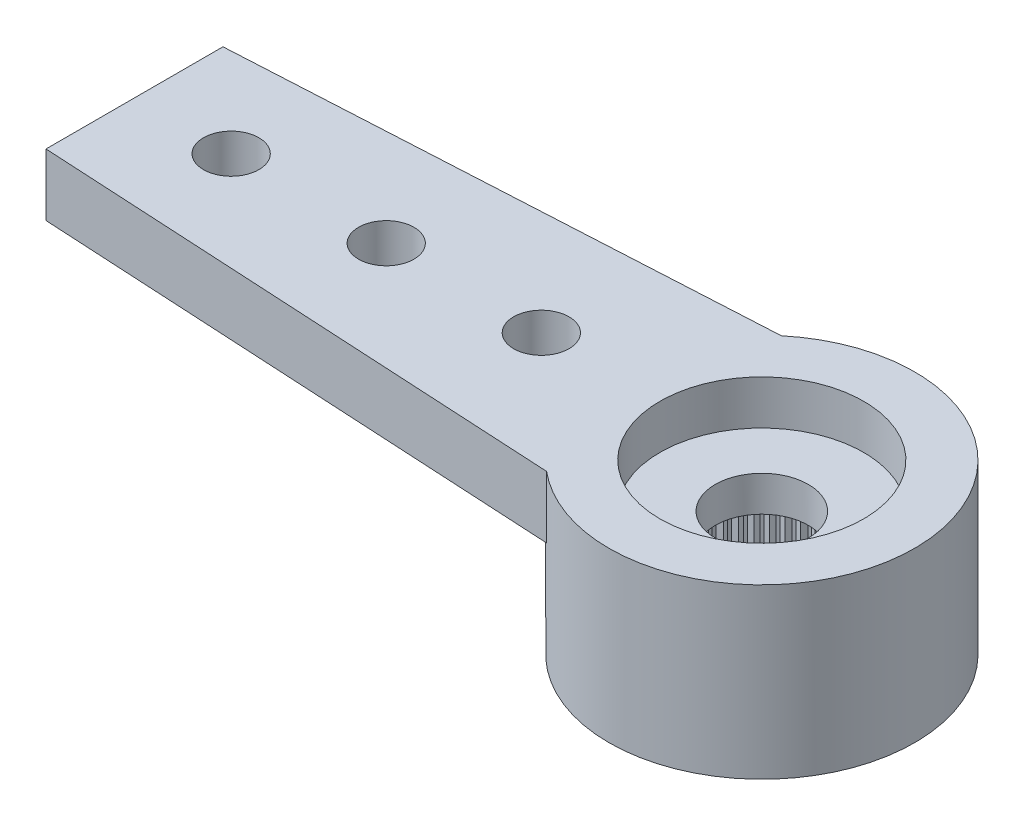
SolidWorks part; units mm, degrees
material "PVC Rígido"
ref_plane "Plano frontal" through (0, 0, 0) normal (0, 0, 1) x (1, 0, 0)
ref_plane "Plano superior" through (0, 0, 0) normal (0, 1, 0) x (1, 0, 0)
ref_plane "Plano direito" through (0, 0, 0) normal (1, 0, 0) x (0, 0, -1)
sketch "Esboço1" plane through (0, 0, 0) normal (0, 1, 0) x (1, 0, 0)
  line L0 (0, 0) -> (-15.7115, 0) construction
  line L1 (-14.1591, 1.997) -> (-2.2091, 2.65)
  line L2 (-2.2091, -2.65) -> (-14.1591, -1.997)
  line L3 (-14.1591, -1.997) -> (-14.1591, 1.997)
  arc A0 (-2.2091, -2.65) -> (-2.2091, 2.65) centre (0, 0) ccw
  dimension "D1" = 6.9
  dimension "D4" = 5.3
extrude "Ressalto-extrusão1" add sketch "Esboço1" against normal blind 1.4
sketch "Esboço2" plane through (0, -1.4, 0) normal (0, -1, 0) x (1, 0, 0)
  arc A0 (-2.2091, -2.65) -> (-2.2091, 2.65) centre (0, 0) ccw construction
  circle A1 centre (0, 0) radius 3.45
extrude "Ressalto-extrusão2" add sketch "Esboço2" along normal offset from surface (2.4 mm away) 3.8 up to face at (-6.7693, 0, 0)
hole_wizard "Furo1" positions "Esboço3" profile "Esboço4" legacy
sketch "Esboço3" plane through (0, -3.8, 0) normal (0, -1, 0) x (-1, 0, 0)
  point P0 (0, 0)
sketch "Esboço4" plane through (0, -3.8, 0) normal (1, 0, 0) x (0, 0, -1)
  line L0 (0, 0) -> (0, 2)
  line L1 (0, 2) -> (2.475, 2)
  line L2 (2.475, 2) -> (2.475, 0)
  line L3 (2.475, 0) -> (0, 0)
  line L4 (0, 110) -> (0, -10) construction
  dimension "Diameter" = 4.95
  dimension "Depth" = 2
hole_wizard "Furo2" positions "Esboço5" profile "Esboço6" legacy
sketch "Esboço5" plane through (0, 0, 0) normal (0, 1, 0) x (1, 0, 0)
  point P0 (0, 0)
sketch "Esboço6" plane through (0, 0, 0) normal (1, 0, 0) x (0, 0, 1)
  line L0 (0, 0) -> (0, 1)
  line L1 (0, 1) -> (2.3, 1)
  line L2 (2.3, 1) -> (2.3, 0)
  line L3 (2.3, 0) -> (0, 0)
  line L4 (0, 110) -> (0, -10) construction
  dimension "Diameter" = 4.6
  dimension "Depth" = 1
hole_wizard "Furo3" positions "Esboço7" profile "Esboço8" legacy end condition through all
sketch "Esboço7" plane through (0, 0, 0) normal (0, 1, 0) x (1, 0, 0)
  point P0 (0, 0)
sketch "Esboço8" plane through (0, 0, 0) normal (1, 0, 0) x (0, 0, 1)
  line L0 (0, 0) -> (0, 3.8)
  line L1 (0, 3.8) -> (1.05, 3.8)
  line L2 (1.05, 3.8) -> (1.05, 0)
  line L3 (1.05, 0) -> (0, 0)
  line L4 (0, 110) -> (0, -10) construction
  dimension "Diameter" = 2.1
  dimension "Depth" = 3.8
sketch "Esboço11" plane through (0, -3.8, 0) normal (0, -1, 0) x (1, 0, 0)
  line L0 (-0.0981, 2.4731) -> (0, 2.375)
  line L1 (0, 2.375) -> (0.0981, 2.4731)
  line L2 (0, 0) -> (0, 2.475) construction
  circle A0 centre (0, 0) radius 2.375 construction
  circle A1 centre (0, 0) radius 2.475
  arc A2 (0.0981, 2.4731) -> (-0.0981, 2.4731) centre (0, 0) ccw
  dimension "D3" = 4.75
  dimension "D2" = 0.1
  dimension "D1" = 0
extrude "Ressalto-extrusão3" add sketch "Esboço11" against normal up to surface (2 mm away) up to face at (0, -1.8, 1.05)
pattern_circular "PadrãoCircular1" count 60 over 360 about axis through (0, 0, 0) along (0, 1, 0) of "Ressalto-extrusão3"
sketch "Esquisse1" plane through (0, 0, 0) normal (0, 1, 0) x (1, 0, 0)
  line L0 (-16.1925, 0) -> (4.8552, 0) construction
  circle A0 centre (-8.4769, 0) radius 0.625
  circle A1 centre (-4.9769, 0) radius 0.625
  circle A2 centre (-11.9769, 0) radius 0.625
  dimension "D1" = 1.25
  dimension "D2" = 3
extrude "Enlèv. mat.-Extru.1" cut sketch "Esquisse1" against normal through all
